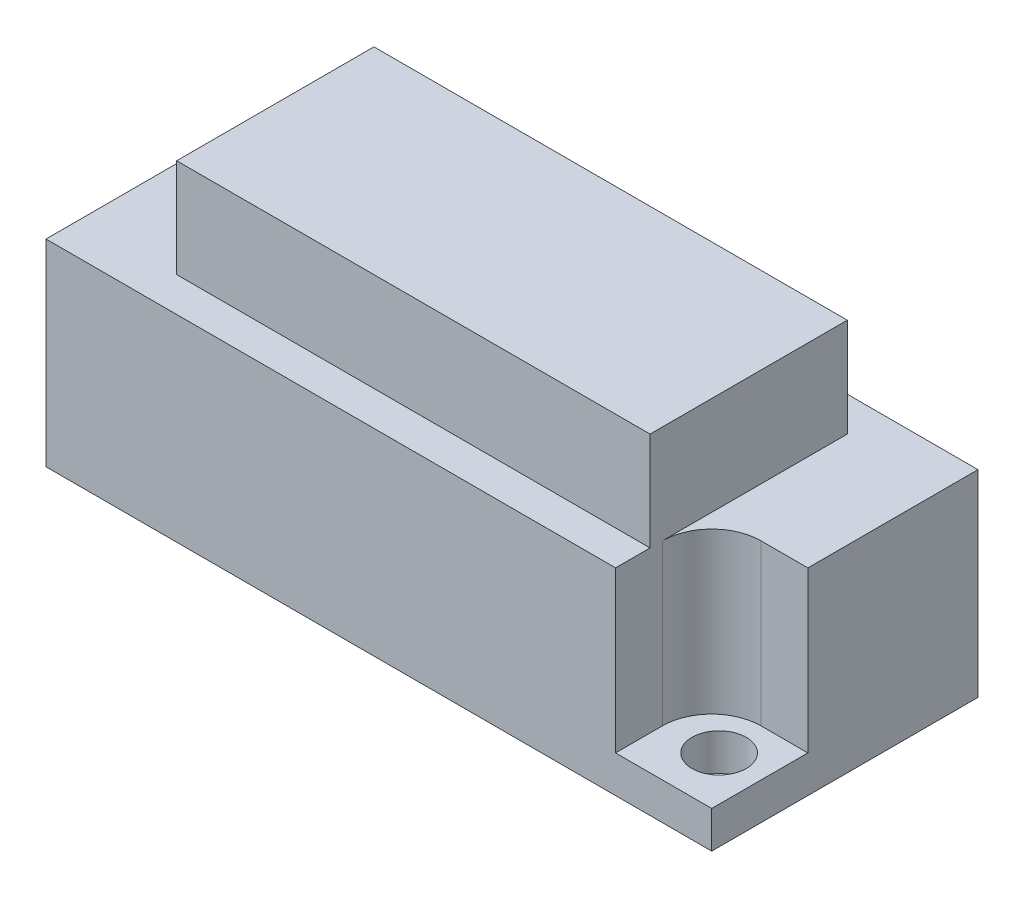
SolidWorks part; units mm, degrees
ref_plane "Front Plane" through (0, 0, 0) normal (0, 0, 1) x (1, 0, 0)
ref_plane "Top Plane" through (0, 0, 0) normal (0, 1, 0) x (1, 0, 0)
ref_plane "Right Plane" through (0, 0, 0) normal (1, 0, 0) x (0, 0, -1)
sketch "스케치1" plane through (0, 0, 0) normal (0, 1, 0) x (1, 0, 0)
  line L1 (-13.5, 5.4) -> (13.5, 5.4)
  line L2 (-13.5, 5.4) -> (-13.5, -5.4)
  line L3 (-13.5, -5.4) -> (13.5, -5.4)
  line L4 (13.5, 5.4) -> (13.5, -5.4)
  point P7 (-52.013, -0.1151)
  dimension "D1" = 27
  dimension "D2" = 10.8
  dimension "D3" = 5.4
  dimension "D4" = 13.5
extrude "보스-돌출1" add sketch "스케치1" along normal blind 12
sketch "스케치2" plane through (0, 12, 0) normal (0, 1, 0) x (1, 0, 0)
  line L1 (-13.5, 5.4) -> (-9.6, 5.4)
  line L2 (-13.5, 5.4) -> (-13.5, 1.5)
  line L3 (-13.5, 1.5) -> (-9.6, 1.5)
  line L4 (-9.6, 5.4) -> (-9.6, 1.5)
  line L5 (13.5, -5.4) -> (9.6, -5.4)
  line L6 (13.5, -5.4) -> (13.5, -1.5)
  line L7 (13.5, -1.5) -> (9.6, -1.5)
  line L8 (9.6, -5.4) -> (9.6, -1.5)
  dimension "D1" = 3.9
  dimension "D2" = 3.9
  dimension "D3" = 3.9
  dimension "D4" = 3.9
extrude "컷-돌출1" cut sketch "스케치2" against normal blind 10.5
fillet "필렛1" radius 2 2 edges at (9.6, 6.75, 1.5) (-9.6, 6.75, -1.5)
sketch "스케치3" plane through (0, 12, 0) normal (0, 1, 0) x (1, 0, 0)
  line L0 (-8.4174, 3.3) -> (49991.5826, 3.3) construction
  line L1 (0.2158, -3.3) -> (50000.2158, -3.3) construction
  line L2 (-11.7, 2.9812) -> (-11.7, -49997.0188) construction
  line L3 (11.7, -2.7114) -> (11.7, 49997.2886) construction
  line L4 (-9.6, 5.4) -> (-13.5, 5.4) construction
  line L5 (9.6, -5.4) -> (13.5, -5.4) construction
  line L6 (13.5, -1.5) -> (13.5, 5.4) construction
  line L7 (-13.5, 5.4) -> (-13.5, 1.5) construction
  circle A0 centre (-11.7, 3.3) radius 1.1
  circle A1 centre (11.7, -3.3) radius 1.1
  dimension "D1" = 2.1
  dimension "D2" = 2.1
  dimension "D3" = 1.8
  dimension "D4" = 1.8
extrude "컷-돌출2" cut sketch "스케치3" against normal blind 40.5
sketch "스케치4" plane through (0, 12, 0) normal (0, 1, 0) x (1, 0, 0)
  line L1 (-9.6, 4) -> (9.6, 4)
  line L2 (-9.6, 4) -> (-9.6, -4)
  line L3 (-9.6, -4) -> (9.6, -4)
  line L4 (9.6, 4) -> (9.6, -4)
  line L5 (-13.5, 5.4) -> (13.5, 5.4)
  line L6 (-13.5, 5.4) -> (-13.5, -5.4)
  line L7 (-13.5, -5.4) -> (13.5, -5.4)
  line L8 (13.5, 5.4) -> (13.5, -5.4)
  dimension "D1" = 8
  dimension "D2" = 4
  dimension "D3" = 19.2
  dimension "D4" = 9.6
extrude "컷-돌출3" cut sketch "스케치4" against normal blind 4
